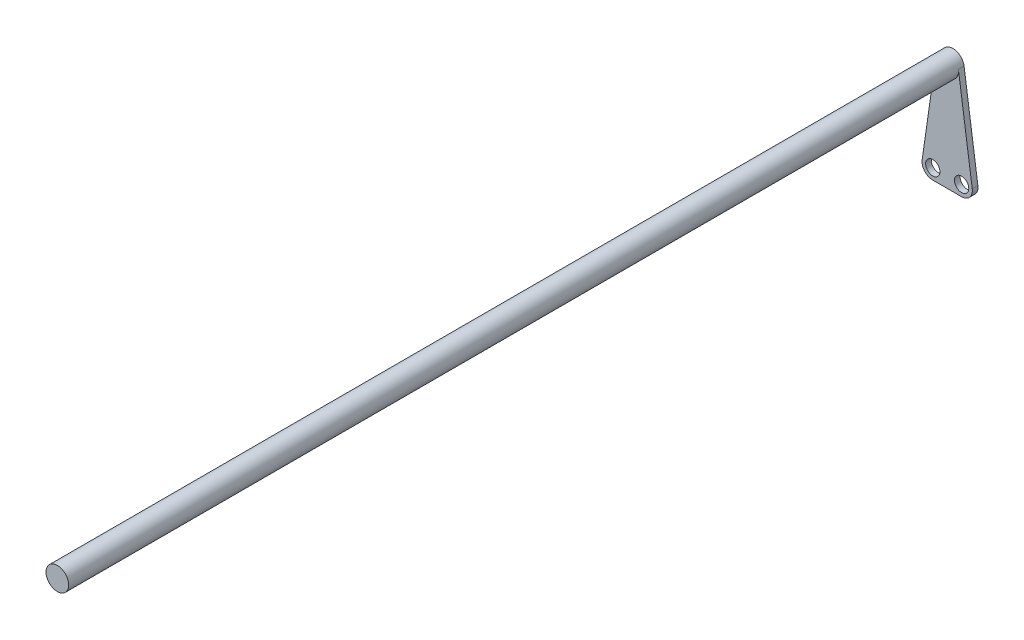
SolidWorks part; units mm, degrees
ref_plane "Front Plane" through (0, 0, 0) normal (0, 0, 1) x (1, 0, 0)
ref_plane "Top Plane" through (0, 0, 0) normal (0, 1, 0) x (1, 0, 0)
ref_plane "Right Plane" through (0, 0, 0) normal (1, 0, 0) x (0, 0, -1)
sketch "Sketch1" plane through (0, 0, 0) normal (0, 0, 1) x (1, 0, 0)
  circle A0 centre (0, 0) radius 6.35
  dimension "D1" = 12.7
extrude "Boss-Extrude1" add sketch "Sketch1" along normal mid plane 500
sketch "Sketch2" plane through (0, 0, -250) normal (0, 0, -1) x (-1, 0, 0)
  line L0 (-6.286, 0.8995) -> (-14.0199, -53.1501)
  line L3 (-8.0804, -60) -> (8.0804, -60)
  line L4 (14.0199, -53.1501) -> (6.286, 0.8995)
  circle A3 centre (0, 0) radius 6.35 construction
  arc A4 (6.286, 0.8995) -> (-6.286, 0.8995) centre (0, 0) ccw
  arc A5 (8.0804, -60) -> (14.0199, -53.1501) centre (8.0804, -54) ccw
  arc A6 (-14.0199, -53.1501) -> (-8.0804, -60) centre (-8.0804, -54) ccw
  point P7 (19.8214, -49.7792)
  point P9 (0, -60)
  point P10 (0, 0)
  point P13 (15, -60)
  point P16 (-15, -60)
  dimension "D1" = 60
  dimension "D3" = 6
  dimension "D2" = 30
extrude "Boss-Extrude2" add sketch "Sketch2" along normal mid plane 3.175
sketch "Sketch3" plane through (0, 0, -248.4125) normal (0, 0, 1) x (1, 0, 0)
  circle A2 centre (-8.0804, -54) radius 4
  circle A3 centre (8.0804, -54) radius 4
  arc A4 (-14.0199, -53.1501) -> (-8.0804, -60) centre (-8.0804, -54) ccw construction
  arc A5 (8.0804, -60) -> (14.0199, -53.1501) centre (8.0804, -54) ccw construction
  dimension "D1" = 8
  dimension "D2" = 8
extrude "Cut-Extrude1" cut sketch "Sketch3" against normal up to next
